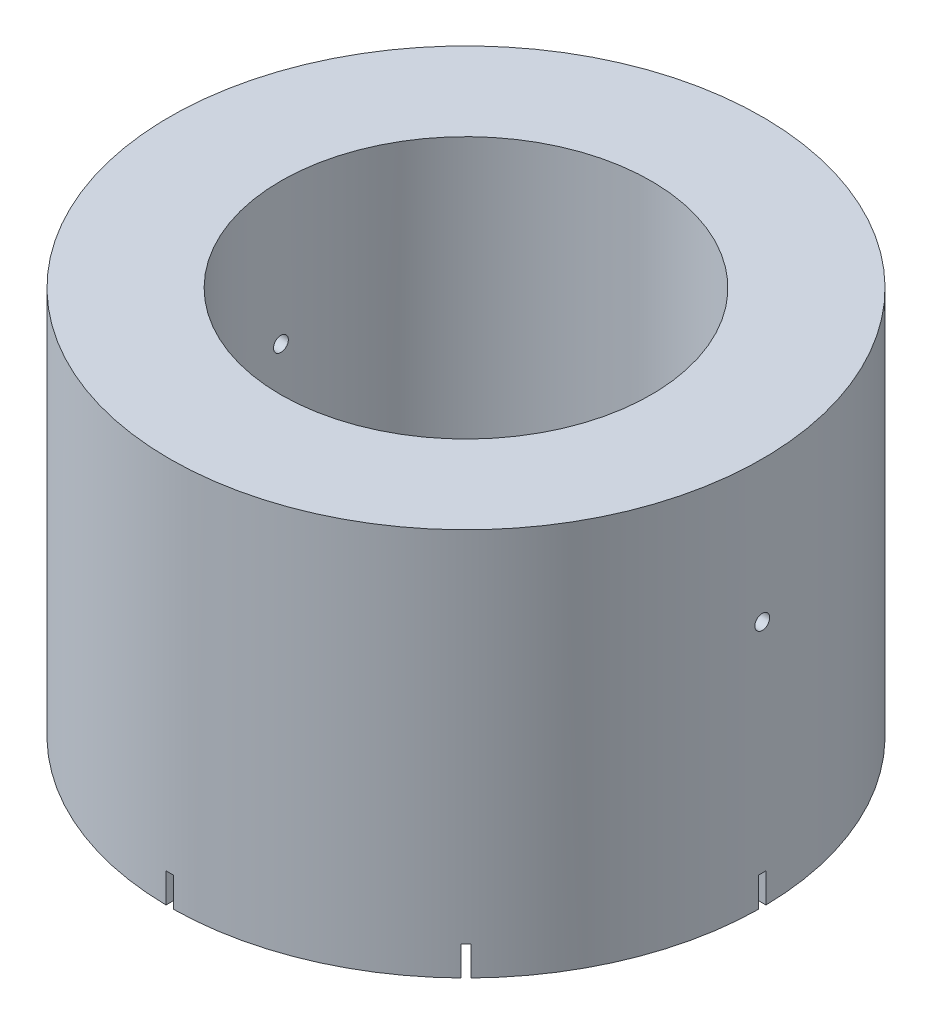
SolidWorks part; units mm, degrees
material "C (Graphite)"
ref_plane "Front Plane" through (0, 0, 0) normal (0, 0, 1) x (1, 0, 0)
ref_plane "Top Plane" through (0, 0, 0) normal (0, 1, 0) x (1, 0, 0)
ref_plane "Right Plane" through (0, 0, 0) normal (1, 0, 0) x (0, 0, -1)
sketch "Sketch1" plane through (0, 0, 0) normal (0, 1, 0) x (1, 0, 0)
  circle A0 centre (0, 0) radius 40
  circle A1 centre (0, 0) radius 25
  dimension "D1" = 80
  dimension "D2" = 50
extrude "Boss-Extrude1" add sketch "Sketch1" along normal blind 50
sketch "Sketch2" plane through (0, 0, 0) normal (0, -1, 0) x (1, 0, 0)
  circle A0 centre (0, 0) radius 37.5
  circle A1 centre (0, 0) radius 40
  dimension "D1" = 75
  dimension "D2" = 80
extrude "Boss-Extrude2" add sketch "Sketch2" along normal blind 5
sketch "Sketch3" plane through (0, 0, 0) normal (1, 0, 0) x (0, 0, -1)
  line L0 (40, 50) -> (-40, 50) construction
  circle A0 centre (0, 30.95) radius 1
  dimension "D1" = 2
  dimension "D2" = 19.05
extrude "Cut-Extrude2" cut sketch "Sketch3" against normal through all both and the other way through all
sketch "Sketch4" plane through (0, 0, 0) normal (0, 0, 1) x (1, 0, 0)
  line L0 (-40, -5) -> (40, -5) construction
  line L1 (-0.5, -5) -> (0.5, -5)
  line L2 (-0.5, -5) -> (-0.5, 1.6)
  line L3 (-0.5, 1.6) -> (0.5, 1.6)
  line L4 (0.5, -5) -> (0.5, 1.6)
  line L5 (0, -30.25) -> (0, 30.25) construction
  point P6 (0, 1.6)
  dimension "D1" = 0
  dimension "D2" = 1
  dimension "D3" = 6.6
extrude "Cut-Extrude3" cut sketch "Sketch4" against normal through all both and the other way through all
pattern_circular "CirPattern1" count 4 every 45 about axis through (0, 0, 0) along (0, 1, 0) of "Cut-Extrude3"
sketch "Sketch5" plane through (0, -5, 0) normal (0, -1, 0) x (1, 0, 0)
  circle A0 centre (0, 0) radius 61.0899
extrude "Cut-Extrude4" cut sketch "Sketch5" against normal blind 2.6
